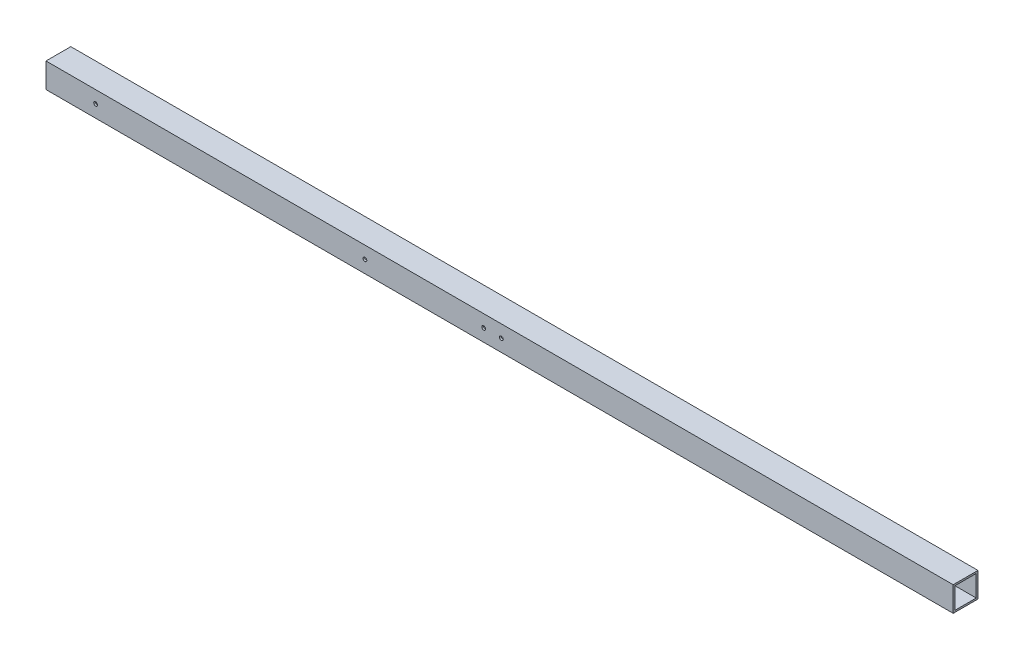
SolidWorks part; units mm, degrees
material "6061 Alloy"
ref_plane "Front Plane" through (0, 0, 0) normal (0, 0, 1) x (1, 0, 0)
ref_plane "Top Plane" through (0, 0, 0) normal (0, 1, 0) x (1, 0, 0)
ref_plane "Right Plane" through (0, 0, 0) normal (1, 0, 0) x (0, 0, -1)
sketch "Sketch1" plane through (0, 0, 0) normal (1, 0, 0) x (0, 0, -1)
  line L1 (0, 0) -> (44.45, 0)
  line L2 (0, 0) -> (0, 44.45)
  line L3 (0, 44.45) -> (44.45, 44.45)
  line L4 (44.45, 0) -> (44.45, 44.45)
  line L5 (3.175, 41.275) -> (41.275, 41.275)
  line L6 (3.175, 41.275) -> (3.175, 3.175)
  line L7 (3.175, 3.175) -> (41.275, 3.175)
  line L8 (41.275, 41.275) -> (41.275, 3.175)
  dimension "D1" = 3.175
  dimension "D2" = 3.175
  dimension "D3" = 44.45
  dimension "D4" = 44.45
  dimension "D5" = 38.1
  dimension "D6" = 38.1
extrude "Boss-Extrude1" add sketch "Sketch1" along normal blind 1625.6
sketch "Sketch2" plane through (0, 0, 0) normal (0, 0, 1) x (1, 0, 0)
  line L0 (1625.6, 44.45) -> (0, 44.45) construction
  line L1 (1625.6, 0) -> (0, 0) construction
  line L3 (0, 44.45) -> (0, 0) construction
  circle A0 centre (784.225, 22.225) radius 3.3734
  circle A1 centre (815.975, 22.225) radius 3.3734
  circle A2 centre (571.5, 22.225) radius 3.3734
  circle A3 centre (88.9, 22.225) radius 3.3734
  dimension "D5" = 6.7469
  dimension "D6" = 6.7469
  dimension "D7" = 212.725
  dimension "D8" = 6.7469
  dimension "D9" = 22.225
  dimension "D10" = 482.6
  dimension "D11" = 6.7469
  dimension "D2" = 31.75
  dimension "D3" = 22.225
  dimension "D4" = 22.225
  dimension "D12" = 22.225
  dimension "D13" = 88.9
extrude "Cut-Extrude1" cut sketch "Sketch2" against normal through all
